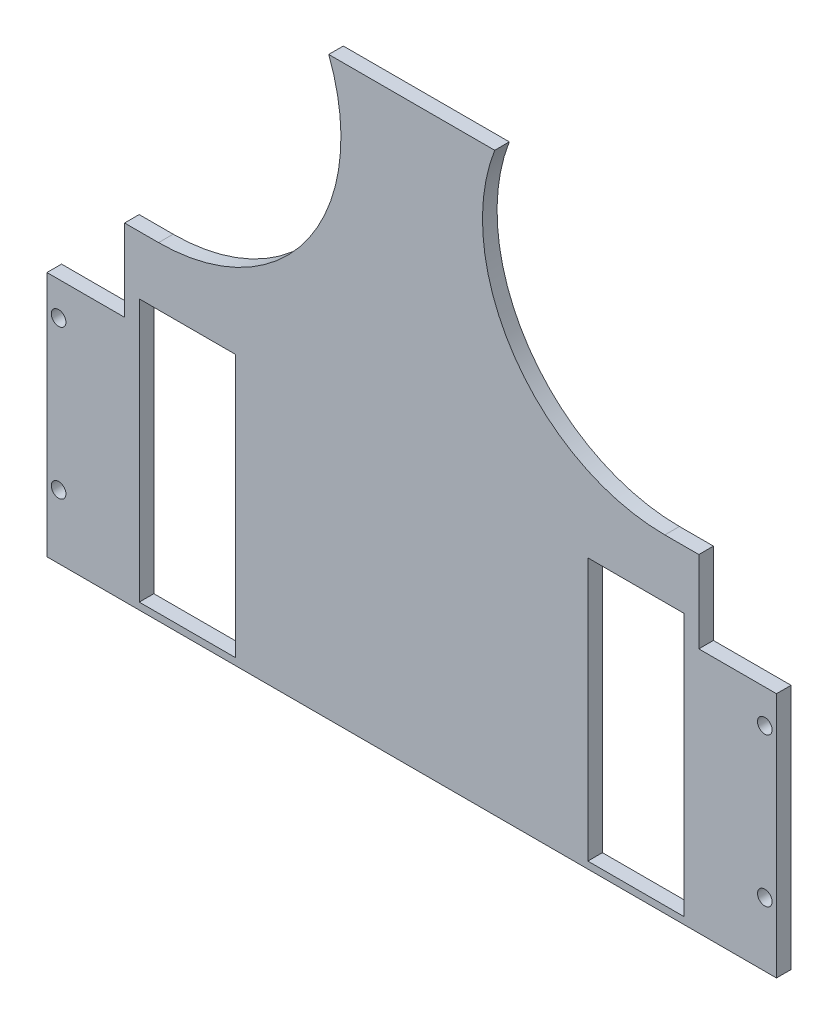
SolidWorks part; units mm, degrees
ref_plane "Front Plane" through (0, 0, 0) normal (0, 0, 1) x (1, 0, 0)
ref_plane "Top Plane" through (0, 0, 0) normal (0, 1, 0) x (1, 0, 0)
ref_plane "Right Plane" through (0, 0, 0) normal (1, 0, 0) x (0, 0, -1)
sketch "Sketch1" plane through (0, 0, 0) normal (0, 0, 1) x (1, 0, 0)
  line L0 (-3272.4324, -69) -> (-3272.4324, -336.4) construction
  line L1 (-3397.4324, -69) -> (-3147.4324, -69)
  line L2 (-3397.4324, -69) -> (-3397.4324, -336.4)
  line L3 (-3397.4324, -336.4) -> (-3147.4324, -336.4)
  line L4 (-3147.4324, -69) -> (-3147.4324, -336.4)
  line L9 (-3212.0724, -174) -> (-3179.0724, -174)
  line L10 (-3212.0724, -174) -> (-3212.0724, -264)
  line L11 (-3212.0724, -264) -> (-3179.0724, -264)
  line L12 (-3179.0724, -174) -> (-3179.0724, -264)
  line L13 (-3248.1828, -69) -> (-3296.682, -69) construction
  line L14 (-3365.7924, -219) -> (-3179.0724, -219) construction
  line L15 (-3147.4324, -336.4) -> (-3147.4324, -182) construction
  line L21 (-3397.4324, -182) -> (-3397.4324, -336.4) construction
  line L25 (-3147.4324, -336.4) -> (-3209.9324, -336.4) construction
  line L52 (-3193.0724, -174) -> (-3193.0724, -264) construction
  line L53 (-3203.0724, -174) -> (-3183.0724, -174) construction
  line L54 (-3203.0724, -174) -> (-3203.0724, -264) construction
  line L55 (-3203.0724, -264) -> (-3183.0724, -264) construction
  line L56 (-3183.0724, -174) -> (-3183.0724, -264) construction
  line L102 (-3151.4324, -193.5) -> (-3151.4324, -244.5) construction
  line L103 (-3179.0724, -219) -> (-3151.4324, -219) construction
  line L134 (-3365.7924, -219) -> (-3393.4324, -219) construction
  line L135 (-3393.4324, -193.5) -> (-3393.4324, -244.5) construction
  line L139 (-3361.7924, -174) -> (-3361.7924, -264) construction
  line L140 (-3341.7924, -264) -> (-3361.7924, -264) construction
  line L141 (-3341.7924, -174) -> (-3341.7924, -264) construction
  line L142 (-3341.7924, -174) -> (-3361.7924, -174) construction
  line L143 (-3351.7924, -174) -> (-3351.7924, -264) construction
  line L154 (-3365.7924, -174) -> (-3365.7924, -264)
  line L155 (-3332.7924, -264) -> (-3365.7924, -264)
  line L156 (-3332.7924, -174) -> (-3332.7924, -264)
  line L157 (-3332.7924, -174) -> (-3365.7924, -174)
  circle A84 centre (-3151.4324, -193.5) radius 2.5
  circle A85 centre (-3151.4324, -244.5) radius 2.5
  circle A236 centre (-3393.4324, -244.5) radius 2.5
  circle A237 centre (-3393.4324, -193.5) radius 2.5
  dimension "D5" = 20
  dimension "D15" = 5
  dimension "D16" = 5
  dimension "D2" = 105
  dimension "D3" = 4
  dimension "D4" = 90
  dimension "D6" = 90
  dimension "D7" = 9
  dimension "D14" = 89.36
  dimension "D17" = 25.5
  dimension "D18" = 4
extrude "Boss-Extrude1" add sketch "Sketch1" along normal blind 5
ref_plane "Plane1"
sketch "Sketch6" plane through (0, 0, 5) normal (0, 0, 1) x (1, 0, 0)
  line L13 (-3147.4324, -336.4) -> (-3147.4324, -69) construction
  line L17 (-3243.9923, -69) -> (-3147.4324, -69)
  line L19 (-3370.8281, -154) -> (-3359.182, -154) construction
  line L24 (-3397.4324, -336.4) -> (-3147.4324, -336.4)
  line L26 (-3397.4324, -336.4) -> (-3397.4324, -266.3756)
  line L27 (-3147.4324, -336.4) -> (-3147.4324, -266.3756)
  line L28 (-3397.4324, -266.3756) -> (-3147.4324, -266.3756)
  line L30 (-3147.4324, -69) -> (-3397.4324, -69) construction
  line L32 (-3147.4324, -69) -> (-3147.4324, -182)
  line L33 (-3147.4324, -336.4) -> (-3147.4324, -69) construction
  line L34 (-3147.4324, -182) -> (-3174.0368, -182)
  line L35 (-3174.0368, -182) -> (-3174.0368, -154)
  line L36 (-3174.0368, -154) -> (-3185.6828, -154)
  line L37 (-3185.6828, -154) -> (-3164.7824, -154) construction
  line L38 (-3300.8725, -69) -> (-3397.4324, -69)
  line L39 (-3397.4324, -69) -> (-3397.4324, -182)
  line L40 (-3397.4324, -69) -> (-3397.4324, -336.4) construction
  line L41 (-3397.4324, -182) -> (-3370.8281, -182)
  line L42 (-3370.8281, -182) -> (-3370.8281, -154)
  line L44 (-3370.8281, -182) -> (-3370.8281, -154) construction
  line L45 (-3370.8281, -154) -> (-3359.182, -154)
  arc A4 (-3359.182, -154) -> (-3296.682, -91.5) centre (-3359.182, -91.5) ccw construction
  arc A5 (-3243.9923, -69) -> (-3185.6828, -154) centre (-3185.6828, -91.5) ccw construction
  arc A6 (-3185.6828, -154) -> (-3243.9923, -69) centre (-3185.6828, -91.5) cw
  arc A7 (-3359.182, -154) -> (-3300.8725, -69) centre (-3359.182, -91.5) ccw
  dimension "D1" = 62.5
extrude "Cut-Extrude4" cut sketch "Sketch6" against normal through all
